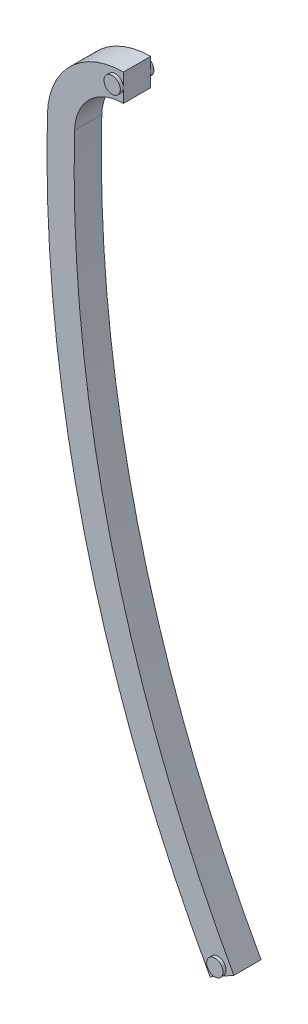
SolidWorks part; units mm, degrees
ref_plane "Front Plane" through (0, 0, 0) normal (0, 0, 1) x (1, 0, 0)
ref_plane "Top Plane" through (0, 0, 0) normal (0, 1, 0) x (1, 0, 0)
ref_plane "Right Plane" through (0, 0, 0) normal (1, 0, 0) x (0, 0, -1)
sketch "Sketch1" plane through (0, 0, 0) normal (0, 0, 1) x (1, 0, 0)
  line L0 (-130.5719, -72.2432) -> (-133.35, -73.7803)
  line L1 (-149.1724, 3.9617) -> (-152.3463, 4.046)
  line L2 (0, 0) -> (-133.35, -73.7803) construction
  line L3 (0, 0) -> (-152.3463, 4.046) construction
  line L4 (-143.4594, 9.525) -> (-143.4594, 12.7)
  line L5 (-143.4594, 12.7) -> (-43.6914, 12.7) construction
  arc A0 (-152.3463, 4.046) -> (-133.35, -73.7803) centre (0, 0) ccw
  arc A1 (-149.1724, 3.9617) -> (-130.5719, -72.2432) centre (0, 0) ccw
  arc A2 (-152.3463, 4.046) -> (-143.4594, 12.7) centre (-143.4594, 3.81) cw
  arc A3 (-149.1724, 3.9617) -> (-143.4594, 9.525) centre (-143.4594, 3.81) cw
  dimension "D1" = 304.8
  dimension "D2" = 3.175
  dimension "D4" = 8.89
  dimension "D3" = 77.8264
  dimension "D5" = 152.3463
extrude "Boss-Extrude1" add sketch "Sketch1" along normal blind 3.175 contours L1 A3 L4 A2 | A1 L1 A0 L0
sketch "Sketch2" plane through (0, 0, 3.175) normal (0, 0, 1) x (1, 0, 0)
  line L0 (-143.4594, 13.97) -> (-143.4594, 12.7)
  line L1 (-133.35, -73.7803) -> (-134.4613, -74.3952)
  arc A0 (-143.4594, 12.7) -> (-152.3463, 4.046) centre (-143.4594, 3.81) ccw construction
  arc A1 (-152.3463, 4.046) -> (-133.35, -73.7803) centre (0, 0) ccw construction
  arc A2 (-143.4594, 12.7) -> (-152.3463, 4.046) centre (-143.4594, 3.81) ccw
  arc A3 (-152.3463, 4.046) -> (-133.35, -73.7803) centre (0, 0) ccw
  arc A4 (-143.4594, 13.97) -> (-153.6158, 4.0797) centre (-143.4594, 3.81) ccw
  arc A5 (-153.6158, 4.0797) -> (-134.4613, -74.3952) centre (0, 0) ccw
  dimension "D1" = 1.27
extrude "Boss-Extrude2" [suppressed] add sketch "Sketch2" against normal blind 5.08
ref_plane "Plane1" through (0, 0, 1.5875) normal (0, 0, -1) x (-1, 0, 0)
sketch "Sketch3" plane through (0, 0, 1.5875) normal (0, 0, -1) x (-1, 0, 0)
  line L3 (143.4594, 11.1125) -> (144.4119, 11.1125) construction
  line L4 (143.4594, 9.525) -> (143.4594, 12.7) construction
  line L5 (131.9609, -73.0118) -> (132.4221, -72.1783) construction
  line L6 (130.5719, -72.2432) -> (133.35, -73.7803) construction
  circle A4 centre (144.4119, 11.1125) radius 0.9525
  circle A5 centre (132.4221, -72.1783) radius 0.9525
  dimension "D1" = 1.905
extrude "Boss-Extrude3" add sketch "Sketch3" along normal mid plane 3.925
